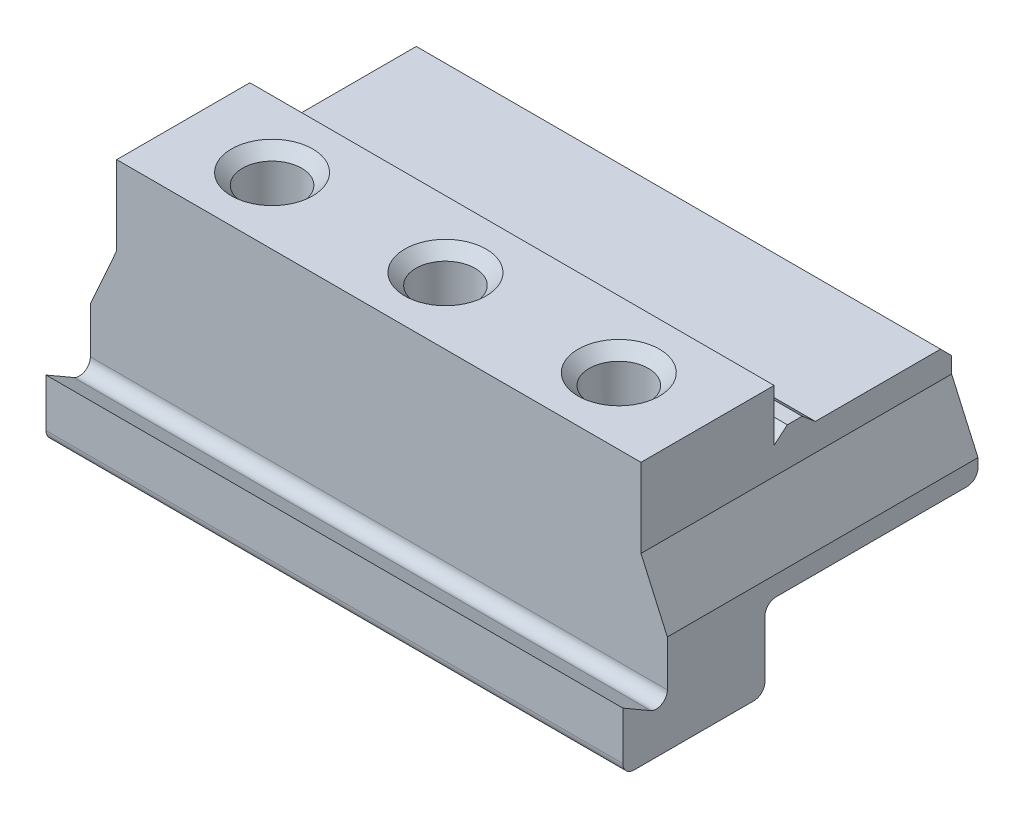
SolidWorks part; units mm, degrees
ref_plane "Front Plane" through (0, 0, 0) normal (0, 0, 1) x (1, 0, 0)
ref_plane "Top Plane" through (0, 0, 0) normal (0, 1, 0) x (1, 0, 0)
ref_plane "Right Plane" through (0, 0, 0) normal (1, 0, 0) x (0, 0, -1)
sketch "Sketch1" plane through (0, 0, 0) normal (0, 1, 0) x (1, 0, 0)
  line L1 (-39, -24) -> (39, -24)
  line L2 (-39, -24) -> (-39, 24)
  line L3 (-39, 24) -> (39, 24)
  line L4 (39, -24) -> (39, 24)
  line L5 (-39, -24) -> (39, 24) construction
  line L6 (-39, 24) -> (39, -24) construction
  point P0 (0, 0)
  dimension "D1" = 78
  dimension "D2" = 48
extrude "Boss-Extrude1" add sketch "Sketch1" along normal blind 32
sketch "Sketch2" plane through (0, 0, 24) normal (0, 0, 1) x (1, 0, 0)
  line L0 (-39, 13.33) -> (-35.4382, 21.33)
  line L1 (-35.4382, 21.33) -> (-35.4382, 32)
  line L3 (35.4382, 21.33) -> (35.4382, 32)
  line L4 (-39, 0) -> (39, 0)
  line L5 (39, 0) -> (39, 32)
  line L6 (39, 32) -> (-39, 32)
  line L7 (-39, 32) -> (-39, 0)
  line L9 (39, 13.33) -> (39, 32)
  line L10 (39, 32) -> (35.4382, 32)
  line L11 (-39, 32) -> (-39, 13.33)
  line L12 (39, 13.33) -> (35.4382, 21.33)
  line L13 (-35.4382, 32) -> (-39, 32)
  dimension "D2" = 24
  dimension "D3" = 8
  dimension "D4" = 10.67
  dimension "D1" = 0
extrude "Cut-Extrude1" cut sketch "Sketch2" against normal through all both and the other way through all
sketch "Sketch3" plane through (39, 0, 0) normal (1, 0, 0) x (0, 0, -1)
  line L0 (-24, 8) -> (-18, 4.5359)
  line L1 (-24, 13.33) -> (-24, 0) construction
  line L2 (-18, 4.5359) -> (-18, 32)
  line L3 (24, 32) -> (-24, 32) construction
  line L4 (2.7876, 26.5) -> (2.7876, 25.4062) construction
  line L5 (-18, 32) -> (0, 32)
  line L6 (0, 32) -> (0, 25)
  line L7 (0, 25) -> (1.7876, 26.5)
  line L8 (1.7876, 26.5) -> (3.7876, 26.5)
  line L9 (3.7876, 26.5) -> (5.5753, 25)
  line L10 (5.5753, 25) -> (24, 25)
  line L11 (24, 32) -> (24, 21.33) construction
  line L12 (24, 25) -> (24, 10.67)
  line L13 (24, 13.33) -> (24, 0) construction
  line L14 (24, 10.67) -> (-4.8, 10.67)
  line L15 (-4.8, 10.67) -> (-4.8, 0)
  line L16 (-24, 0) -> (24, 0) construction
  line L17 (-4.8, 0) -> (-24, 0)
  line L18 (-24, 0) -> (-24, 8)
  line L19 (24, 21.33) -> (-24, 21.33) construction
  point P26 (5.8066, 25)
  dimension "D1" = 28.8
  dimension "D2" = 6
  dimension "D3" = 10.67
  dimension "D4" = 7
  dimension "D5" = 18
  dimension "D6" = 60
  dimension "D7" = 8
  dimension "D8" = 40
  dimension "D9" = 2
  dimension "D10" = 1.5
extrude "Cut-Extrude3" cut sketch "Sketch3" against normal through all both and the other way through all flip side to cut
fillet "Fillet1" radius 1.5 5 edges at (0, 10.67, -24) (0, 10.67, 4.8) (0, 0, 4.8) (0, 0, 24) (0, 4.5359, 18)
sketch "Sketch4" plane through (0, 32, 0) normal (0, 1, 0) x (1, 0, 0)
  line L0 (0, 0) -> (0, -18) construction
  line L1 (-35.4382, 0) -> (35.4382, 0) construction
  line L2 (-35.4382, -18) -> (35.4382, -18) construction
  line L3 (0, -9) -> (35.4382, -9) construction
  line L4 (35.4382, 0) -> (35.4382, -18) construction
  line L5 (35.4382, -9) -> (-35.4382, -9) construction
  line L6 (-35.4382, 0) -> (-35.4382, -18) construction
  circle A0 centre (0, -9) radius 4
  circle A1 centre (23.4382, -9) radius 4
  circle A2 centre (-23.4382, -9) radius 4
  dimension "D1" = 8
  dimension "D2" = 12
extrude "Cut-Extrude4" cut sketch "Sketch4" against normal blind 10 and the other way through all
chamfer "Chamfer1" distance 1.5 angle 45 4 edges at (0, 25, -24) (-23.4382, 32, 5) (0, 32, 5) (23.4382, 32, 5)
